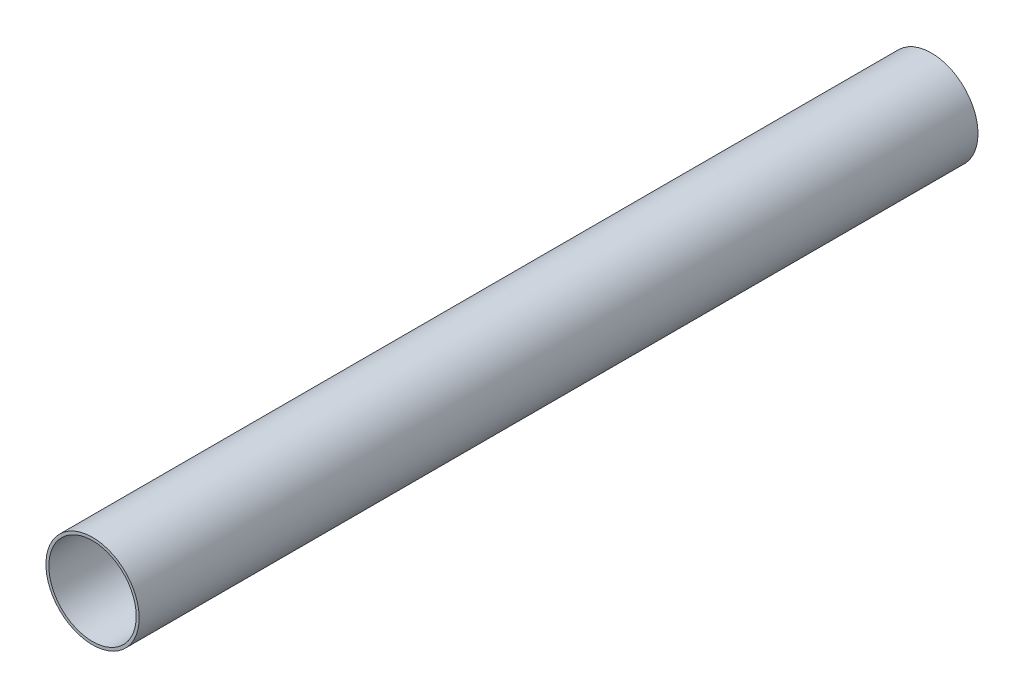
SolidWorks part; units mm, degrees
ref_plane "Front" through (0, 0, 0) normal (0, 0, 1) x (1, 0, 0)
ref_plane "Top" through (0, 0, 0) normal (0, 1, 0) x (1, 0, 0)
ref_plane "Side" through (0, 0, 0) normal (1, 0, 0) x (0, 0, -1)
sketch "PipeSketch" plane through (0, 0, 0) normal (0, 0, 1) x (1, 0, 0)
  circle A0 centre (0, 0) radius 304.8
  circle A1 centre (0, 0) radius 285.75
  dimension "OuterDiameter" = 609.6
  dimension "InnerDiameter" = 571.5
extrude "Extrusion" add sketch "PipeSketch" along normal blind 5486.4
sketch "FilterSketch" plane through (0, 0, 0) normal (0, 0, 1) x (1, 0, 0)
  circle A0 centre (0, 0) radius 304.8 construction
  dimension "NominalDiameter" = 609.6
